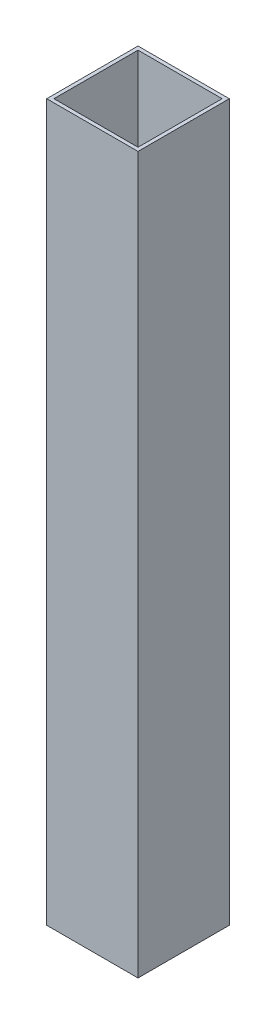
SolidWorks part; units mm, degrees
ref_plane "Front Plane" through (0, 0, 0) normal (0, 0, 1) x (1, 0, 0)
ref_plane "Top Plane" through (0, 0, 0) normal (0, 1, 0) x (1, 0, 0)
ref_plane "Right Plane" through (0, 0, 0) normal (1, 0, 0) x (0, 0, -1)
sketch "Sketch1" plane through (0, 0, 0) normal (0, 1, 0) x (1, 0, 0)
  line L1 (0, 0) -> (25.4, 0)
  line L2 (0, 0) -> (0, -25.4)
  line L3 (0, -25.4) -> (25.4, -25.4)
  line L4 (25.4, 0) -> (25.4, -25.4)
  line L5 (1, -1) -> (24.4, -1)
  line L6 (1, -1) -> (1, -24.4)
  line L7 (1, -24.4) -> (24.4, -24.4)
  line L8 (24.4, -1) -> (24.4, -24.4)
  dimension "D1" = 25.4
  dimension "D2" = 25.4
  dimension "D3" = 1
  dimension "D4" = 1
  dimension "D5" = 1
  dimension "D6" = 1
extrude "Boss-Extrude1" add sketch "Sketch1" along normal blind 199.2
